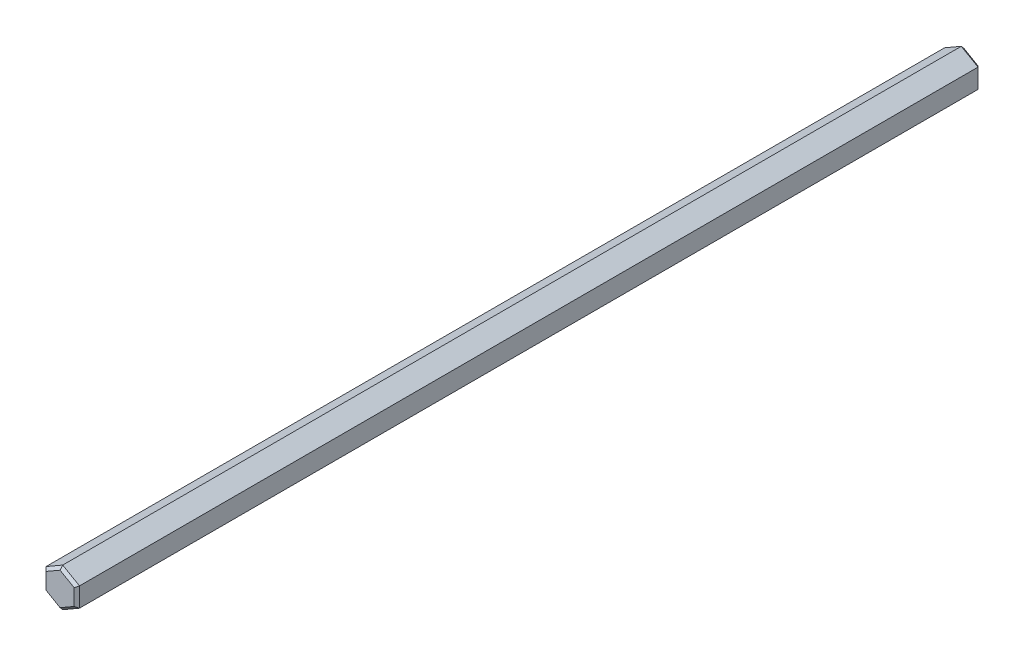
SolidWorks part; units mm, degrees
material "Plain Carbon Steel"
ref_plane "Front Plane" through (0, 0, 0) normal (0, 0, 1) x (1, 0, 0)
ref_plane "Top Plane" through (0, 0, 0) normal (0, 1, 0) x (1, 0, 0)
ref_plane "Right Plane" through (0, 0, 0) normal (1, 0, 0) x (0, 0, -1)
ref_plane "Plane1" through (0, 0, 67.5) normal (0, 0, 1) x (1, 0, 0)
sketch "Sketch1" plane through (0, 0, 67.5) normal (0, 0, 1) x (1, 0, 0)
  line L0 (0, -2.8868) -> (2.5, -1.4434)
  line L1 (2.5, -1.4434) -> (2.5, 1.4434)
  line L2 (2.5, 1.4434) -> (0, 2.8868)
  line L3 (0, 2.8868) -> (-2.5, 1.4434)
  line L4 (-2.5, 1.4434) -> (-2.5, -1.4434)
  line L5 (-2.5, -1.4434) -> (0, -2.8868)
extrude "Boss-Extrude1" add sketch "Sketch1" against normal blind 135
chamfer "Chamfer1" distance 0.4 angle 45 12 edges at (-2.5, 0, -67.5) (-1.25, -2.1651, -67.5) (-1.25, 2.1651, -67.5) (1.25, -2.1651, -67.5) (1.25, 2.1651, -67.5) (2.5, 0, -67.5) (-1.25, 2.1651, 67.5) (-2.5, 0, 67.5) (1.25, 2.1651, 67.5) (-1.25, -2.1651, 67.5) (2.5, 0, 67.5) (1.25, -2.1651, 67.5)
